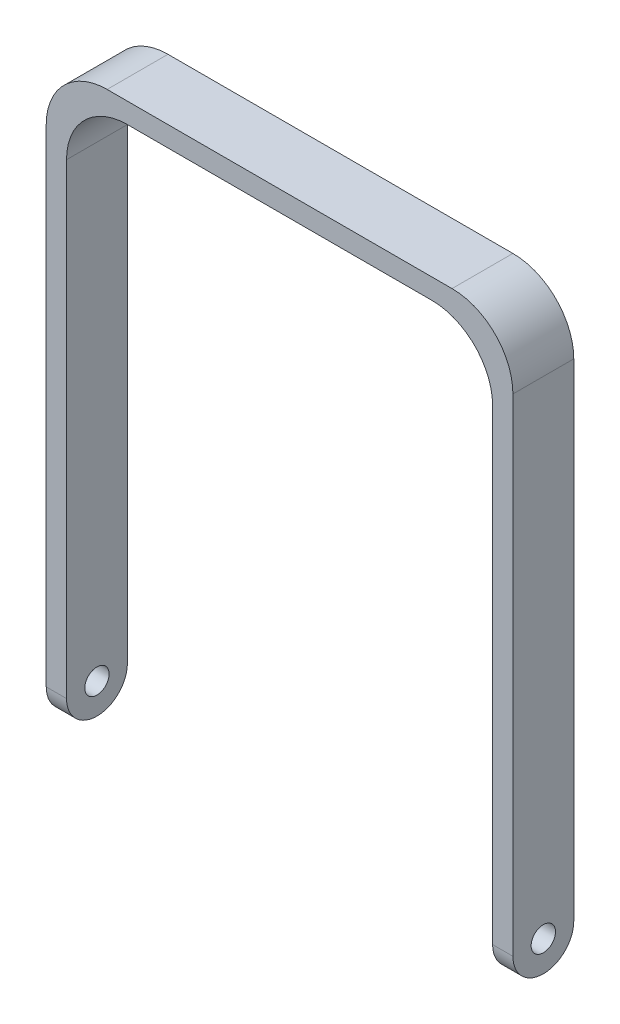
SolidWorks part; units mm, degrees
ref_plane "Front Plane" through (0, 0, 0) normal (0, 0, 1) x (1, 0, 0)
ref_plane "Top Plane" through (0, 0, 0) normal (0, 1, 0) x (1, 0, 0)
ref_plane "Right Plane" through (0, 0, 0) normal (1, 0, 0) x (0, 0, -1)
sketch "Sketch1" plane through (0, 0, 0) normal (0, 0, 1) x (1, 0, 0)
  line L0 (33.3375, -46.0375) -> (36.5125, -46.0375)
  line L1 (-36.5125, -46.0375) -> (-33.3375, -46.0375)
  line L2 (-36.5125, -46.0375) -> (-36.5125, 46.0375)
  line L3 (-36.5125, 46.0375) -> (36.5125, 46.0375)
  line L4 (36.5125, -46.0375) -> (36.5125, 46.0375)
  line L5 (-36.5125, -46.0375) -> (36.5125, 46.0375) construction
  line L6 (-36.5125, 46.0375) -> (36.5125, -46.0375) construction
  line L8 (33.3375, -46.0375) -> (33.3375, 42.8625)
  line L9 (33.3375, 42.8625) -> (-33.3375, 42.8625)
  line L10 (-33.3375, -46.0375) -> (-33.3375, 42.8625)
  point P0 (0, 0)
  point P10 (-77.6802, -46.6572)
  point P11 (-30.5939, -47.8834)
  point P12 (32.4332, -48.006)
  point P13 (31.5748, 41.0166)
  point P14 (0, 42.8625)
  point P15 (0, 46.0375)
  dimension "D1" = 88.9
  dimension "D2" = 66.675
  dimension "D3" = 3.175
  dimension "D4" = 3.175
extrude "Boss-Extrude1" add sketch "Sketch1" along normal mid plane 9.525
sketch "Sketch2" plane through (-36.5125, 0, 0) normal (-1, 0, 0) x (0, 0, 1)
  line L0 (0, 42.8625) -> (0, -39.6875) construction
  line L1 (4.7625, 42.8625) -> (-4.7625, 42.8625) construction
  line L2 (-4.7625, 46.0375) -> (-4.7625, -46.0375) construction
  line L3 (4.7625, 46.0375) -> (4.7625, -46.0375) construction
  line L4 (-4.7625, -39.6875) -> (-4.7625, -46.0375)
  line L5 (-4.7625, -46.0375) -> (4.7625, -46.0375)
  line L6 (4.7625, -46.0375) -> (4.7625, -39.6875)
  circle A0 centre (0, -39.6875) radius 1.905
  arc A1 (-4.7625, -39.6875) -> (4.7625, -39.6875) centre (0, -39.6875) ccw
  dimension "D2" = 3.81
  dimension "D1" = 82.55
extrude "Cut-Extrude1" cut sketch "Sketch2" against normal through all both and the other way through all
fillet "Fillet1" radius 9.525 4 edges at (-33.3375, 42.8625, 0) (-36.5125, 46.0375, 0) (36.5125, 46.0375, 0) (33.3375, 42.8625, 0)
